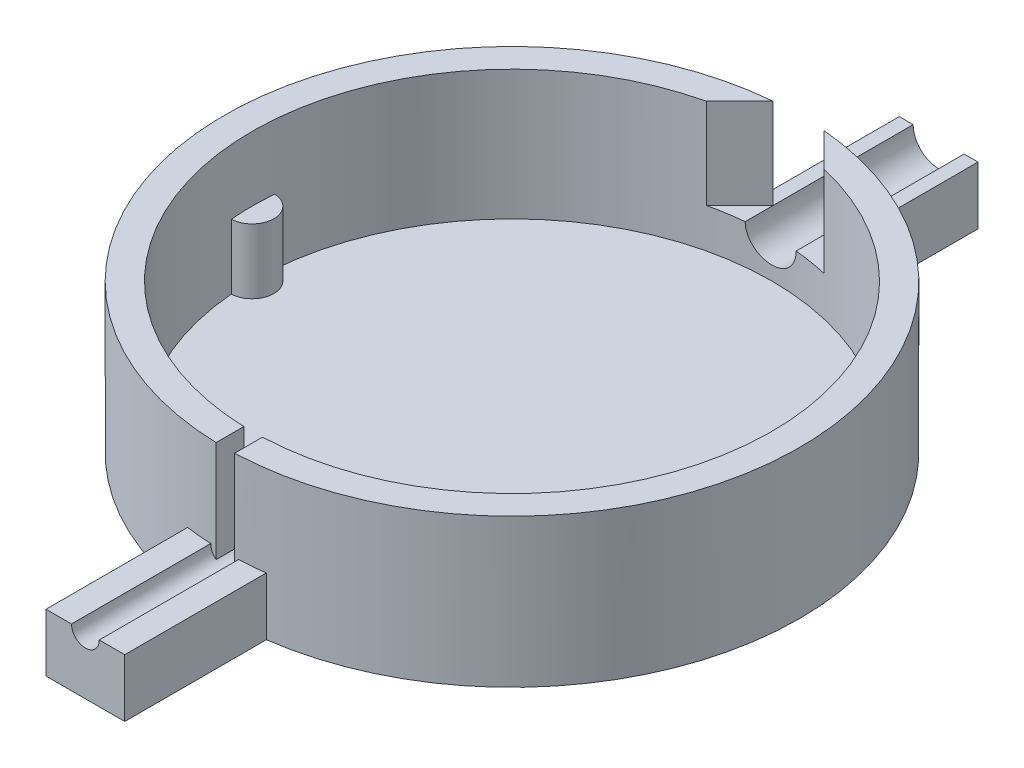
SolidWorks part; units mm, degrees
ref_plane "Front Plane" through (0, 0, 0) normal (0, 0, 1) x (1, 0, 0)
ref_plane "Top Plane" through (0, 0, 0) normal (0, 1, 0) x (1, 0, 0)
ref_plane "Right Plane" through (0, 0, 0) normal (1, 0, 0) x (0, 0, -1)
sketch "Sketch1" plane through (0, 0, 0) normal (0, 1, 0) x (1, 0, 0)
  circle A0 centre (0, 0) radius 31.06
  dimension "D1" = 62.12
extrude "Boss-Extrude1" add sketch "Sketch1" along normal blind 16
sketch "Sketch2" plane through (0, 16, 0) normal (0, 1, 0) x (1, 0, 0)
  circle A0 centre (0, 0) radius 28.06
  circle A1 centre (0, 0) radius 31.06 construction
  circle A2 centre (0, 0) radius 31.06
  dimension "D1" = 3
extrude "Cut-Extrude1" cut sketch "Sketch2" against normal blind 14 contours A0
sketch "Sketch3" plane through (0, 2, 0) normal (0, 1, 0) x (1, 0, 0)
  arc A0 (-27.9616, -2.3479) -> (-27.9616, 2.3479) centre (-28.06, 0) ccw
  circle A1 centre (0, 0) radius 28.06 construction
  arc A2 (27.9616, 2.3479) -> (27.9616, -2.3479) centre (28.06, 0) ccw
  arc A3 (27.9616, -2.3479) -> (27.9616, 2.3479) centre (0, 0) ccw
  arc A4 (-27.9616, 2.3479) -> (-27.9616, -2.3479) centre (0, 0) ccw
  dimension "D1" = 4.7
  dimension "D2" = 4.7
extrude "Boss-Extrude2" add sketch "Sketch3" along normal blind 7
sketch "Sketch4" plane through (0, 0, 0) normal (0, 0, 1) x (1, 0, 0)
  line L0 (27.9616, 2) -> (-27.9616, 2) construction
  line L1 (27.9616, 2) -> (-27.9616, 2)
  line L2 (0, 0) -> (0, 4.7714)
  line L3 (28.06, 16) -> (-28.06, 16) construction
  line L4 (28.06, 16) -> (-28.06, 16)
  line L5 (-2.75, 6.25) -> (-2.75, 16)
  line L6 (2.75, 6.25) -> (2.75, 16)
  circle A0 centre (0, 6.25) radius 2.75
  dimension "D1" = 5.5
  dimension "D2" = 4.25
extrude "Cut-Extrude2" cut sketch "Sketch4" against normal through all contours A0 L6 L4 L5
sketch "Sketch5" plane through (0, 0, 0) normal (0, 0, 1) x (1, 0, 0)
  line L0 (28.06, 16) -> (-28.06, 16) construction
  line L1 (1.0982, 3.999) -> (-0.9018, 3.999)
  line L2 (1.0982, 3.999) -> (1.0982, 16)
  line L3 (1.0982, 5.999) -> (-0.9018, 5.999)
  line L4 (-0.9018, 3.999) -> (-0.9018, 16)
  line L5 (1.0982, 3.999) -> (-0.9018, 5.999) construction
  line L6 (1.0982, 5.999) -> (-0.9018, 3.999) construction
  line L7 (1.0982, 16) -> (-0.9018, 16)
  point P0 (0.0982, 4.999)
  dimension "D1" = 2
  dimension "D2" = 2
  dimension "D3" = 5
extrude "Cut-Extrude3" cut sketch "Sketch5" along normal through all contours L2 L7 L4 L1
ref_plane "Plane1" through (0, 0, -28.06) normal (0, 0, 1) x (1, 0, 0)
sketch "Sketch6" plane through (0, 0, -28.06) normal (0, 0, 1) x (1, 0, 0)
  line L0 (-31.06, 0) -> (31.06, 0) construction
  line L1 (-4.25, 0) -> (4.25, 0)
  line L2 (4.25, 6.25) -> (4.25, 0)
  line L3 (-4.25, 6.25) -> (-4.25, 0)
  line L4 (-4.25, 6.25) -> (-2.75, 6.25)
  line L5 (-2.75, 6.25) -> (-2.7454, 6.232)
  line L6 (2.75, 6.25) -> (4.25, 6.25)
  arc A0 (-2.75, 6.25) -> (2.75, 6.25) centre (0, 6.25) ccw construction
  arc A1 (-2.75, 6.25) -> (2.75, 6.25) centre (0, 6.25) ccw
extrude "Boss-Extrude3" add sketch "Sketch6" against normal blind 18 contours A1 L6 L2 L1 L3 L4
ref_plane "Plane2" through (0, 0, 28.06) normal (0, 0, -1) x (-1, 0, 0)
sketch "Sketch7" plane through (0, 0, 28.06) normal (0, 0, -1) x (-1, 0, 0)
  line L5 (4.25, 6.25) -> (2.75, 6.25)
  line L6 (-2.75, 6.25) -> (-4.25, 6.25)
  line L7 (-4.25, 6.25) -> (-4.25, 0)
  line L8 (-4.25, 0) -> (4.25, 0)
  line L9 (4.25, 0) -> (4.25, 6.25)
  line L10 (4.25, 6.25) -> (1.5, 6.25)
  line L11 (-1.5, 6.25) -> (-4.25, 6.25)
  line L12 (-4.25, 6.25) -> (-4.25, 0)
  line L13 (-4.25, 0) -> (4.25, 0)
  line L14 (4.25, 0) -> (4.25, 6.25)
  arc A0 (-1.5, 6.25) -> (1.5, 6.25) centre (0, 6.25) ccw
  arc A1 (-2.75, 6.25) -> (2.75, 6.25) centre (0, 6.25) ccw
  dimension "D2" = 3
  dimension "D1" = 0
extrude "Boss-Extrude4" add sketch "Sketch7" against normal blind 18
sketch "Sketch8" plane through (0, 16, 0) normal (0, 1, 0) x (1, 0, 0)
  line L0 (2.75, 27.9249) -> (2.75, 30.938) construction
  line L1 (-2.75, 27.9249) -> (-2.75, 30.938) construction
  line L2 (2.75, 27.9249) -> (2.75, 30.938)
  line L3 (-2.75, 27.9249) -> (-2.75, 30.938)
  line L4 (-2.75, 30.938) -> (-6.3578, 27.3302)
  line L5 (2.75, 30.938) -> (6.3578, 27.3302)
  arc A0 (-2.75, 27.9249) -> (-0.9018, -28.0455) centre (0, 0) ccw construction
  arc A1 (1.0982, -28.0385) -> (2.75, 27.9249) centre (0, 0) ccw construction
  arc A2 (-2.75, 27.9249) -> (-6.3578, 27.3302) centre (0, 0) ccw
  arc A3 (6.3578, 27.3302) -> (2.75, 27.9249) centre (0, 0) ccw
  dimension "D1" = 45
  dimension "D2" = 45
extrude "Cut-Extrude4" cut sketch "Sketch8" against normal up to surface (9.75 mm away) up to face at (3.5003, 6.25, -38.4587)
